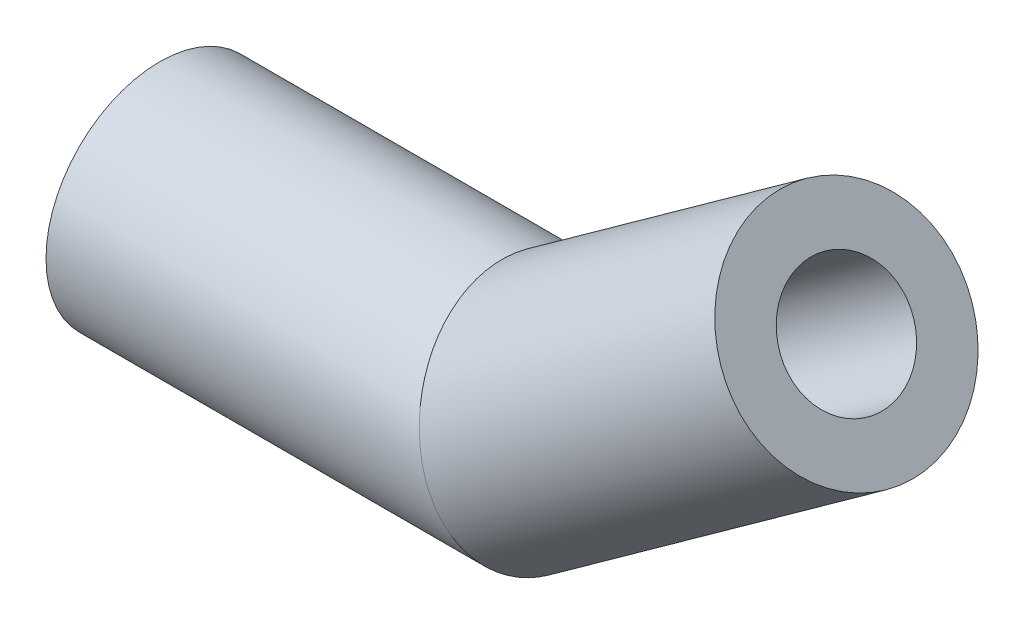
SolidWorks part; units mm, degrees
ref_plane "Front Plane" through (0, 0, 0) normal (0, 0, 1) x (1, 0, 0)
ref_plane "Top Plane" through (0, 0, 0) normal (0, 1, 0) x (1, 0, 0)
ref_plane "Right Plane" through (0, 0, 0) normal (1, 0, 0) x (0, 0, -1)
sketch "Sketch2" plane through (0, 0, 0) normal (0, 0, 1) x (1, 0, 0)
  line L0 (0, 0) -> (10, 0)
  line L1 (10, 0) -> (18.1198, 5.8368)
  dimension "D1" = 10
  dimension "D2" = 10
  dimension "D3" = 144.29
sketch "Sketch3" plane through (0, 0, 0) normal (1, 0, 0) x (0, 0, -1)
  circle A0 centre (0, 0) radius 1.6
  circle A1 centre (0, 0) radius 3
  dimension "D1" = 3.2
  dimension "D2" = 6
sweep "Sweep1" add path "Sketch2" circular profile diameter 6 parameters "D3"=6
extrude "Cut-Extrude1" cut sketch "Sketch3" along normal blind 7 contours A0
sketch "Sketch10" plane through (0, 0, 0) normal (0, 0, 1) x (1, 0, 0)
  line L0 (10.0626, -0.1944) -> (8.1127, 5.8588) construction
ref_plane "Plane2" through (9.0599, 2.9184, 0) normal (0.9518, 0.3066, 0) x (-0.3066, 0.9518, 0)
mirror "Mirror1" about plane through (9.0599, 2.9184, 0) normal (0.9518, 0.3066, 0) of "Cut-Extrude1"
